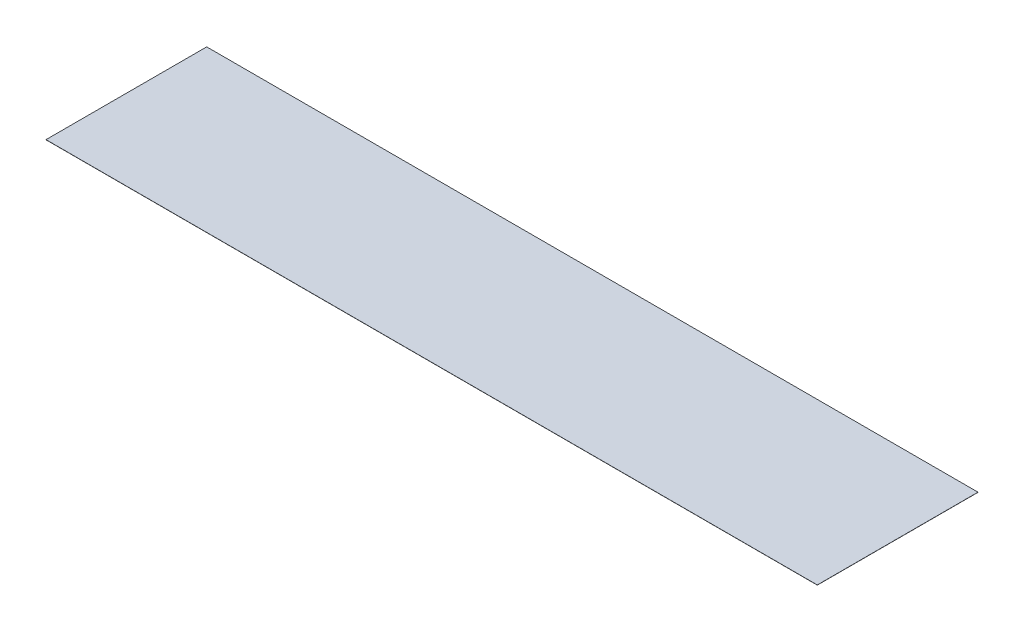
SolidWorks part; units mm, degrees
ref_plane "Front Plane" through (0, 0, 0) normal (0, 0, 1) x (1, 0, 0)
ref_plane "Top Plane" through (0, 0, 0) normal (0, 1, 0) x (1, 0, 0)
ref_plane "Right Plane" through (0, 0, 0) normal (1, 0, 0) x (0, 0, -1)
sketch "Sketch1" plane through (0, 0, 0) normal (0, 1, 0) x (1, 0, 0)
  line L1 (-10972.8, 0) -> (10972.8, 0)
  line L2 (-10972.8, 0) -> (-10972.8, 4572)
  line L3 (-10972.8, 4572) -> (10972.8, 4572)
  line L4 (10972.8, 0) -> (10972.8, 4572)
  point P5 (0, 0)
  dimension "D1" = 4572
  dimension "D2" = 21945.6
extrude "Boss-Extrude1" add sketch "Sketch1" along normal blind 4.7752
ref_plane "Plane1" through (0, 0, 0) normal (1, 0, 0) x (0, 0, -1)
